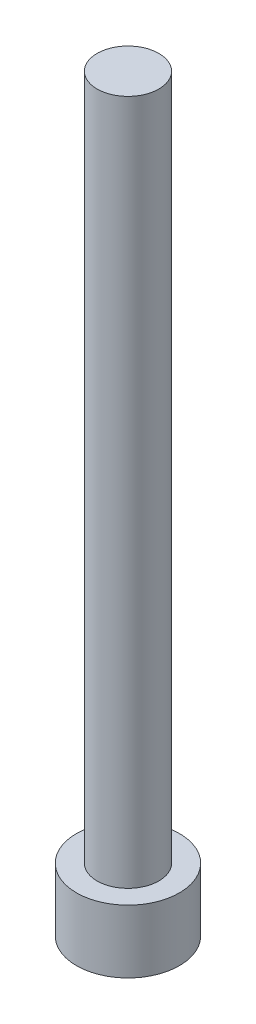
SolidWorks part; units mm, degrees
ref_plane "Front Plane" through (0, 0, 0) normal (0, 0, 1) x (1, 0, 0)
ref_plane "Top Plane" through (0, 0, 0) normal (0, 1, 0) x (1, 0, 0)
ref_plane "Right Plane" through (0, 0, 0) normal (1, 0, 0) x (0, 0, -1)
sketch "Sketch1" plane through (0, 0, 0) normal (0, 1, 0) x (1, 0, 0)
  circle A0 centre (0, 0) radius 2.8575
  dimension "D1" = 5.715
extrude "Boss-Extrude1" add sketch "Sketch1" along normal blind 3.5052
sketch "Sketch2" plane through (0, 0, 0) normal (0, -1, 0) x (1, 0, 0)
  line L1 (1.604, 0) -> (0.802, 1.3891)
  line L2 (0.802, 1.3891) -> (-0.802, 1.3891)
  line L3 (-0.802, 1.3891) -> (-1.604, 0)
  line L4 (-1.604, 0) -> (-0.802, -1.3891)
  line L5 (-0.802, -1.3891) -> (0.802, -1.3891)
  line L6 (0.802, -1.3891) -> (1.604, 0)
  circle A0 centre (0, 0) radius 1.3891 construction
  dimension "D1" = 2.7781
extrude "Cut-Extrude1" cut sketch "Sketch2" against normal blind 1.9558
sketch "Sketch3" plane through (0, 3.5052, 0) normal (0, 1, 0) x (1, 0, 0)
  circle A0 centre (0, 0) radius 1.7145
  dimension "D1" = 3.429
extrude "Boss-Extrude2" add sketch "Sketch3" along normal blind 38.1
